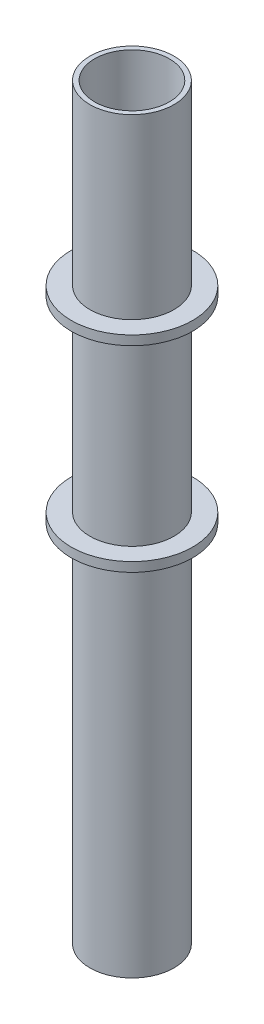
SolidWorks part; units mm, degrees
material "AISI 316 Stainless Steel Sheet (SS)"
ref_plane "Front Plane" through (0, 0, 0) normal (0, 0, 1) x (1, 0, 0)
ref_plane "Top Plane" through (0, 0, 0) normal (0, 1, 0) x (1, 0, 0)
ref_plane "Right Plane" through (0, 0, 0) normal (1, 0, 0) x (0, 0, -1)
sketch "Sketch1" plane through (0, 0, 0) normal (0, 1, 0) x (1, 0, 0)
  circle A0 centre (0, 0) radius 22.5
  circle A1 centre (0, 0) radius 20
  dimension "D1" = 45
  dimension "D2" = 40
extrude "Boss-Extrude1" add sketch "Sketch1" along normal mid plane 400
ref_plane "Plane1" through (0, 100, 0) normal (0, 1, 0) x (1, 0, 0)
sketch "Sketch2" plane through (0, 100, 0) normal (0, 1, 0) x (1, 0, 0)
  circle A0 centre (0, 0) radius 22.5 construction
  circle A1 centre (0, 0) radius 22.5
  circle A2 centre (0, 0) radius 32.5
  dimension "D1" = 65
extrude "Boss-Extrude2" add sketch "Sketch2" along normal blind 5
sketch "Sketch3" plane through (0, 0, 0) normal (0, 1, 0) x (1, 0, 0)
  circle A0 centre (0, 0) radius 22.5 construction
  circle A1 centre (0, 0) radius 32.5
  circle A2 centre (0, 0) radius 32.5
  circle A3 centre (0, 0) radius 22.5
  dimension "D1" = 0
extrude "Boss-Extrude3" add sketch "Sketch3" against normal blind 5
